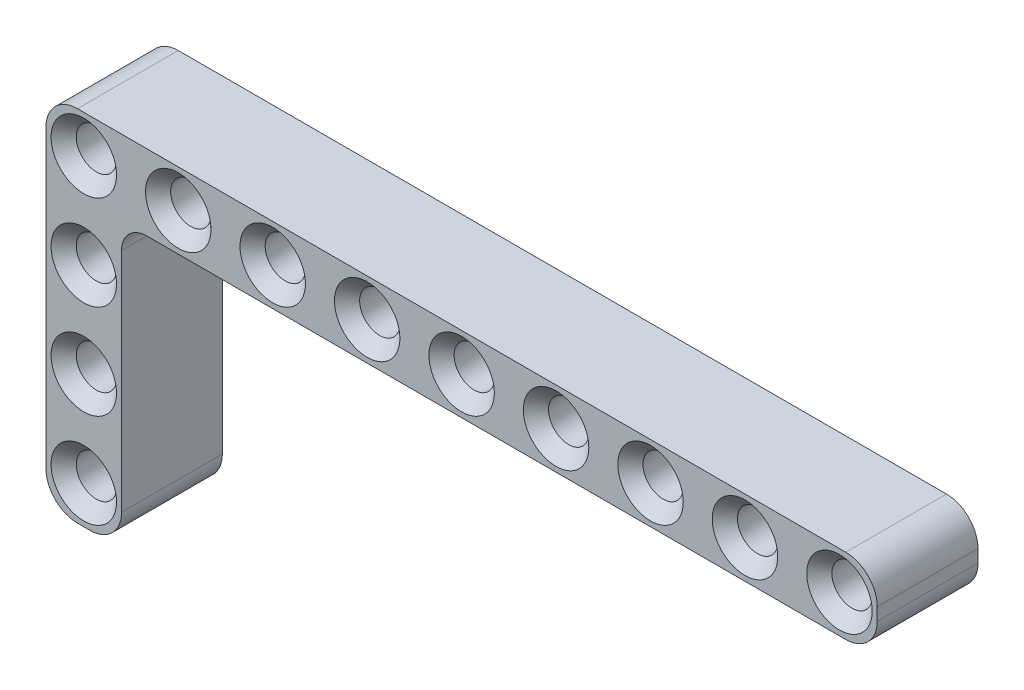
SolidWorks part; units mm, degrees
ref_plane "Front Plane" through (0, 0, 0) normal (0, 0, 1) x (1, 0, 0)
ref_plane "Top Plane" through (0, 0, 0) normal (0, 1, 0) x (1, 0, 0)
ref_plane "Right Plane" through (0, 0, 0) normal (1, 0, 0) x (0, 0, -1)
sketch "Sketch1" plane through (0, 0, 0) normal (0, 0, 1) x (1, 0, 0)
  line L1 (-0.5, 3) -> (60.5, 3)
  line L2 (-3, 0.5) -> (-3, -0.5)
  line L3 (-0.5, -3) -> (60.5, -3)
  line L4 (63, 0.5) -> (63, -0.5)
  circle A0 centre (0, 0) radius 1.6
  arc A1 (60.5, -3) -> (63, -0.5) centre (60.5, -0.5) ccw
  arc A2 (60.5, 3) -> (63, 0.5) centre (60.5, 0.5) cw
  arc A3 (-3, -0.5) -> (-0.5, -3) centre (-0.5, -0.5) ccw
  arc A4 (-0.5, 3) -> (-3, 0.5) centre (-0.5, 0.5) ccw
  circle A5 centre (7.5, 0) radius 1.6
  circle A6 centre (15, 0) radius 1.6
  circle A7 centre (22.5, 0) radius 1.6
  circle A8 centre (30, 0) radius 1.6
  circle A9 centre (37.5, 0) radius 1.6
  circle A10 centre (45, 0) radius 1.6
  circle A11 centre (52.5, 0) radius 1.6
  circle A12 centre (60, 0) radius 1.6
  point P8 (-3, 0)
  point P14 (-3, -3)
  point P17 (-3, 3)
  dimension "D1" = 3.2
  dimension "D4" = 2.5
  dimension "D2" = 6
  dimension "D3" = 3
  dimension "D6" = 7.5
  dimension "D5" = 9
extrude "Boss-Extrude1" add sketch "Sketch1" along normal blind 8
chamfer "Chamfer1" distance 1 angle 45 10 edges at (31.6, 0, 0) (31.6, 0, 8) (24.1, 0, 0) (24.1, 0, 8) (16.6, 0, 0) (16.6, 0, 8) (9.1, 0, 0) (9.1, 0, 8) (1.6, 0, 0) (1.6, 0, 8)
sketch "Sketch2" plane through (0, 0, 8) normal (0, 0, 1) x (1, 0, 0)
  line L0 (-3, 0) -> (-3, -23)
  line L1 (-0.5, -25.5) -> (0.5, -25.5)
  line L2 (3, -23) -> (3, -3)
  line L3 (-3, 0.5) -> (-3, -0.5) construction
  line L4 (-0.5, -3) -> (60.5, -3) construction
  circle A1 centre (0, -7.5) radius 1.6
  arc A4 (-3, -23) -> (-0.5, -25.5) centre (-0.5, -23) ccw
  arc A5 (0.5, -25.5) -> (3, -23) centre (0.5, -23) ccw
  circle A6 centre (0, -15) radius 1.6
  circle A7 centre (0, -22.5) radius 1.6
  point P18 (-3, -25.5)
  point P21 (3, -25.5)
  dimension "D3" = 3.2
  dimension "D8" = 2.5
  dimension "D1" = 6
  dimension "D2" = 90
  dimension "D4" = 3
  dimension "D5" = 7.5
  dimension "D7" = 3
  dimension "D6" = 3
extrude "Boss-Extrude3" add sketch "Sketch2" against normal blind 8
fillet "Fillet1" radius 2 1 edges at (3, -3, 4)
chamfer "Chamfer3" distance 1 angle 45 4 edges at (46.6, 0, 0) (46.6, 0, 8) (39.1, 0, 0) (39.1, 0, 8)
chamfer "Chamfer4" distance 1 angle 45 4 edges at (61.6, 0, 0) (61.6, 0, 8) (54.1, 0, 0) (54.1, 0, 8)
chamfer "Chamfer5" distance 1 angle 45 6 edges at (1.6, -7.5, 8) (1.6, -7.5, 0) (1.6, -15, 8) (1.6, -15, 0) (1.6, -22.5, 8) (1.6, -22.5, 0)
